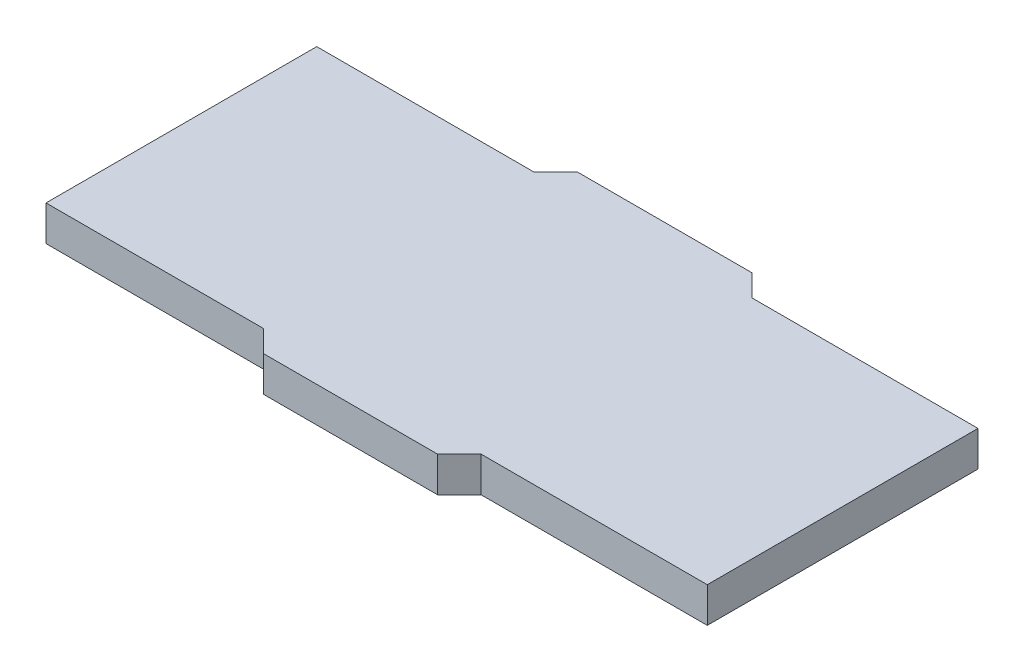
SolidWorks part; units mm, degrees
ref_plane "Front Plane" through (0, 0, 0) normal (0, 0, 1) x (1, 0, 0)
ref_plane "Top Plane" through (0, 0, 0) normal (0, 1, 0) x (1, 0, 0)
ref_plane "Right Plane" through (0, 0, 0) normal (1, 0, 0) x (0, 0, -1)
sketch "Sketch1" plane through (0, 0, 0) normal (0, 1, 0) x (1, 0, 0)
  line L0 (0, -6.223) -> (10, -6.223)
  line L1 (20, -6.223) -> (30.4, -6.223)
  line L2 (30.4, -6.223) -> (30.4, 6.223)
  line L3 (30.4, 6.223) -> (20, 6.223)
  line L4 (10, 6.223) -> (0, 6.223)
  line L5 (0, 6.223) -> (0, -6.223)
  line L6 (10, 6.223) -> (11, 7.223)
  line L7 (11, 7.223) -> (19, 7.223)
  line L8 (19, 7.223) -> (20, 6.223)
  line L9 (10, -6.223) -> (11, -7.223)
  line L10 (11, -7.223) -> (19, -7.223)
  line L11 (19, -7.223) -> (20, -6.223)
  line L12 (0, 0) -> (30.4, 0) construction
  arc A0 (10, -6.2738) -> (10, -6.1722) centre (10, -6.223) ccw
  arc A1 (0, -6.1722) -> (0, -6.2738) centre (0, -6.223) ccw
  arc A2 (30.4, -6.2738) -> (30.4, -6.1722) centre (30.4, -6.223) ccw
  arc A3 (20, -6.1722) -> (20, -6.2738) centre (20, -6.223) ccw
  arc A4 (30.4508, 6.223) -> (30.3492, 6.223) centre (30.4, 6.223) ccw
  arc A5 (30.3492, -6.223) -> (30.4508, -6.223) centre (30.4, -6.223) ccw
  arc A6 (20, 6.2738) -> (20, 6.1722) centre (20, 6.223) ccw
  arc A7 (30.4, 6.1722) -> (30.4, 6.2738) centre (30.4, 6.223) ccw
  arc A8 (0, 6.2738) -> (0, 6.1722) centre (0, 6.223) ccw
  arc A9 (10, 6.1722) -> (10, 6.2738) centre (10, 6.223) ccw
  arc A10 (-0.0508, -6.223) -> (0.0508, -6.223) centre (0, -6.223) ccw
  arc A11 (0.0508, 6.223) -> (-0.0508, 6.223) centre (0, 6.223) ccw
  arc A12 (11.0359, 7.1871) -> (10.9641, 7.2589) centre (11, 7.223) ccw
  arc A13 (9.9641, 6.2589) -> (10.0359, 6.1871) centre (10, 6.223) ccw
  arc A14 (19, 7.1722) -> (19, 7.2738) centre (19, 7.223) ccw
  arc A15 (11, 7.2738) -> (11, 7.1722) centre (11, 7.223) ccw
  arc A16 (19.9641, 6.1871) -> (20.0359, 6.2589) centre (20, 6.223) ccw
  arc A17 (19.0359, 7.2589) -> (18.9641, 7.1871) centre (19, 7.223) ccw
  arc A18 (10.9641, -7.2589) -> (11.0359, -7.1871) centre (11, -7.223) ccw
  arc A19 (10.0359, -6.1871) -> (9.9641, -6.2589) centre (10, -6.223) ccw
  arc A20 (19, -7.2738) -> (19, -7.1722) centre (19, -7.223) ccw
  arc A21 (11, -7.1722) -> (11, -7.2738) centre (11, -7.223) ccw
  arc A22 (20.0359, -6.2589) -> (19.9641, -6.1871) centre (20, -6.223) ccw
  arc A23 (18.9641, -7.1871) -> (19.0359, -7.2589) centre (19, -7.223) ccw
extrude "Boss-Extrude1" add sketch "Sketch1" along normal blind 1.62 contours L4 L5 L0 L9 L10 L11 L1 L2 L3 L8 L7 L6
